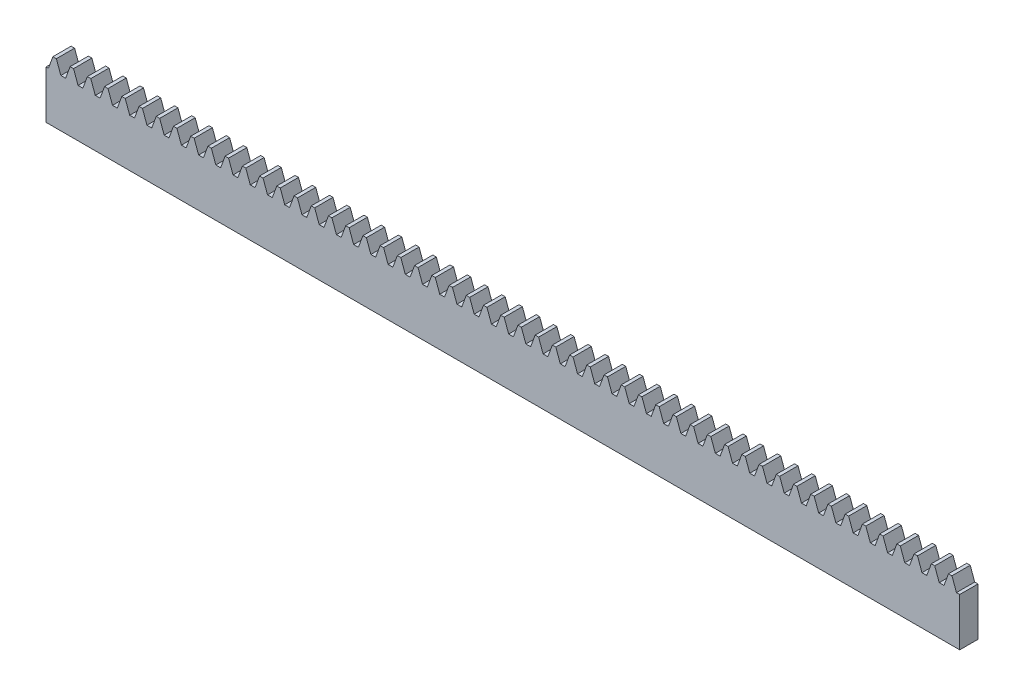
SolidWorks part; units mm, degrees
extrude "Blank" add sketch "BlankSke" against normal blind 5
sketch "BlankSke" plane through (0, 0, 0) normal (0, 0, 1) x (1, 0, 0)
  line L1 (0, 0) -> (250, 0)
  line L2 (0, 0) -> (0, 16.5)
  line L3 (0, 16.5) -> (250, 16.5)
  line L4 (250, 0) -> (250, 16.5)
  dimension "Length" = 250
  dimension "Blank_height" = 16.5
material "Acrylic (Medium-high impact)"
ref_plane "Plane1" through (0, 0, 0) normal (0, 0, 1) x (1, 0, 0)
ref_plane "Plane2" through (0, 0, 0) normal (0, 1, 0) x (1, 0, 0)
ref_plane "Plane3" through (0, 0, 0) normal (1, 0, 0) x (0, 0, -1)
other "Configuration Table"
sketch "HoldingSke" plane through (0, 0, 0) normal (0, 1, 0) x (1, 0, 0)
  line L0 (0, 0) -> (0.0928, 0.6602)
  line L1 (-15, 0) -> (100, 0) construction
  line L2 (0, 0) -> (-2.1039, 2.3779)
  line L3 (0, 0) -> (-11.863, 4.5341)
  line L4 (0, 0) -> (4.9534, 7.0742)
  line L5 (0, 0) -> (-23.7986, -8.8762)
  line L6 (0, 0) -> (-10.5278, -7.1032)
  line L9 (-71.009, 38.7566) -> (163.9142, 124.2616)
  line L10 (-76.2, 3.8779) -> (-61.2, 3.8779)
  line L11 (0, 0) -> (-5, 0)
  line L12 (-76.2, 101.6) -> (-76.147, 101.6)
  line L13 (24.9733, 27.94) -> (52.9518, 28.4284)
  line L14 (24.9733, 27.94) -> (24.9743, 27.94)
  line L15 (24.9733, 27.94) -> (100.4006, 29.5858)
  circle A0 centre (0, 0) radius 19.05
  circle A1 centre (0, 0) radius 7.5
  circle A2 centre (0, 0) radius 12.7
  dimension "MPH" = 15
  dimension "Diameter" = 38.1
  dimension "Num_teeth" = 55
  dimension "Pitch" = 0.6667
  dimension "Show_teeth" = 998
  dimension "Thickness" = 12.7
  dimension "Ap" = 20
  dimension "Pitch_height" = 15
  dimension "Width" = 5
  dimension "Backlash" = 0.053
  dimension "Addendum_fac" = 1
  dimension "Dedendum_fac" = 1.25
  dimension "Clearance_fac" = 0.25
  dimension "Dedendum_add" = 0.001
  dimension "Length" = 250
  dimension "Module" = 1.5
sketch "TooCutSkeIll" plane through (0, 0, 0) normal (0, 0, 1) x (1, 0, 0)
  line L0 (-1.8687, 16.4605) -> (-0.7447, 13.3724)
  line L1 (-0.3914, 13.125) -> (0.3914, 13.125)
  line L2 (0.7447, 13.3724) -> (1.8687, 16.4605)
  line L3 (250, 16.5) -> (0, 16.5) construction
  line L4 (0, 0) -> (0, 64.897) construction
  line L5 (-13.208, 15) -> (12.954, 15) construction
  line L6 (0, 0) -> (250, 0) construction
  line L7 (1.3371, 15) -> (1.3371, 48.7463) construction
  line L8 (-1.3371, 15) -> (-1.3371, 48.7463) construction
  line L9 (1.9251, 16.5) -> (1.9251, 16.5254)
  line L10 (-1.9251, 16.5) -> (-1.9251, 16.5254)
  line L11 (-1.9251, 16.5254) -> (1.9251, 16.5254)
  arc A0 (0.3914, 13.125) -> (0.7447, 13.3724) centre (0.3914, 13.501) ccw
  arc A1 (-0.7447, 13.3724) -> (-0.3914, 13.125) centre (-0.3914, 13.501) ccw
  arc A2 (1.9251, 16.5) -> (1.8687, 16.4605) centre (1.9251, 16.44) ccw
  arc A3 (-1.8687, 16.4605) -> (-1.9251, 16.5) centre (-1.9251, 16.44) ccw
  dimension "Pitch_height" = 15
  dimension "Addendum_plus" = 1.5254
  dimension "Pressure_angle" = 20
  dimension "Gap_width" = 2.6742
  dimension "Dedendum" = 1.875
extrude "ToothCutIll" [suppressed] cut sketch "TooCutSkeIll" against normal through all
sketch "TooCutSkeSim" plane through (0, 0, 0) normal (0, 0, 1) x (1, 0, 0)
  line L0 (0.6547, 13.125) -> (-0.6547, 13.125)
  line L1 (1.8923, 16.5254) -> (0.6547, 13.125)
  line L2 (0, 17.4625) -> (0, 53.467) construction
  line L3 (1.8923, 16.5254) -> (-1.8923, 16.5254)
  line L6 (-1.8923, 16.5254) -> (-0.6547, 13.125)
  line L9 (-1.3371, 15) -> (1.3371, 15) construction
  line L10 (0, 0) -> (250, 0) construction
  line L11 (1.3371, 15) -> (1.3371, 53.467) construction
  line L12 (-1.3371, 15) -> (-1.3371, 53.467) construction
  dimension "Pitch_height" = 15
  dimension "Addendum_plus" = 1.5254
  dimension "Pressure_angle" = 20
  dimension "Gap_width" = 2.6742
  dimension "Dedendum" = 1.875
extrude "ToothCutSim" cut sketch "TooCutSkeSim" against normal through all
pattern_linear "TeethCuts" count 54 spacing 4.7124 along (1, 0, 0) of "ToothCutIll", "ToothCutSim"
equation "' \"Module@HoldingSke\" = 6.35"
equation "' \"Num_teeth@HoldingSke\" = 12"
equation "' \"Ap@HoldingSke\" =  20"
equation "' \"Ap@HoldingSke\" = 20"
equation "' \"Width@HoldingSke\" = 0.25 * 25.4"
equation "' \"Show_teeth@HoldingSke\" = 500"
equation "' \"Backlash@HoldingSke\" = 0.009 * 25.4"
equation "' \"Addendum_fac@HoldingSke\" = 1.0"
equation "' \"Dedendum_fac@HoldingSke\" = 1.25"
equation "' \"Dedendum_add@HoldingSke\" = 0.00005 * 25.4"
equation "' \"Clearance_fac@HoldingSke\" = 0.25"
equation "' \"Pitch_height@HoldingSke\" = 1 * 25.4"
equation "' \"Length@HoldingSke\" = 4.71 * 25.4"
equation "\"Pitch@HoldingSke\" = 1 / \"Module@HoldingSke\""
equation "\"MPH@HoldingSke\" = \"Dedendum_fac@HoldingSke\" / \"Pitch@HoldingSke\" + 2 * \"Dedendum_add@HoldingSke\" + 0.002 * 25.4"
equation "\"MPH@HoldingSke\" = ((sgn( \"MPH@HoldingSke\" - \"Pitch_height@HoldingSke\")+1)*( \"MPH@HoldingSke\" - \"Pitch_height@HoldingSke\"))/2 + \"Pitch_height@HoldingSke\""
equation "\"Blank_height@BlankSke\" = \"Pitch_height@HoldingSke\" + \"Addendum_fac@HoldingSke\"  / \"Pitch@HoldingSke\" "
equation "\"Length@BlankSke\" =  \"Length@HoldingSke\""
equation "\"Face_width@Blank\" = \"Width@HoldingSke\""
equation "\"Pressure_angle@TooCutSkeIll\" = \"Ap@HoldingSke\""
equation "\"Addendum_plus@TooCutSkeIll\" =  \"Addendum_fac@HoldingSke\"  / \"Pitch@HoldingSke\" + 0.001 *25.4"
equation "\"Dedendum@TooCutSkeIll\" = \"Dedendum_fac@HoldingSke\"  / \"Pitch@HoldingSke\""
equation "\"Pitch_height@TooCutSkeIll\" =  \"MPH@HoldingSke\""
equation "\"Gap_width@TooCutSkeIll\" = 3.14159265 / 2 / \"Pitch@HoldingSke\" + 6 * \"Backlash@HoldingSke\""
equation "\"Pressure_angle@TooCutSkeSim\" = \"Ap@HoldingSke\""
equation "\"Addendum_plus@TooCutSkeSim\" =  \"Addendum_fac@HoldingSke\"  / \"Pitch@HoldingSke\" + 0.001 * 25.4"
equation "\"Dedendum@TooCutSkeSim\" = \"Dedendum_fac@HoldingSke\"  / \"Pitch@HoldingSke\""
equation "\"Pitch_height@TooCutSkeSim\" =  \"MPH@HoldingSke\""
equation "\"Gap_width@TooCutSkeSim\" = 3.14159265 / 2 / \"Pitch@HoldingSke\" + 6 * \"Backlash@HoldingSke\""
equation "\"Root_fillet@TooCutSkeIll\" = \"Clearance_fac@HoldingSke\" / \"Pitch@HoldingSke\" + \"Dedendum_add@HoldingSke\""
equation "\"Break_rad@TooCutSkeIll\" = 0.02 / \"Pitch@HoldingSke\" * 2"
equation "\"Linear_pitch@TeethCuts\" = 3.14159265 / \"Pitch@HoldingSke\""
equation "\"Num_teeth@HoldingSke\" = int( ( \"Length@HoldingSke\" + 0 ) / (3.14159265 / \"Pitch@HoldingSke\")) + 0.9999  + 1"
equation " \"Num_teeth@TeethCuts\" = int( \"Show_teeth@HoldingSke\" ) + 1"
equation " \"Num_teeth@TeethCuts\" = ((sgn( \"Num_teeth@TeethCuts\" - \"Num_teeth@HoldingSke\" )-1)*( \"Num_teeth@TeethCuts\" - \"Num_teeth@HoldingSke\" ))/-2+ \"Num_teeth@HoldingSke\""
equation " \"Num_teeth@TeethCuts\" = ((sgn( \"Num_teeth@TeethCuts\" - 2.0)+1)*( \"Num_teeth@TeethCuts\" - 2.0))/2 +2.0"
